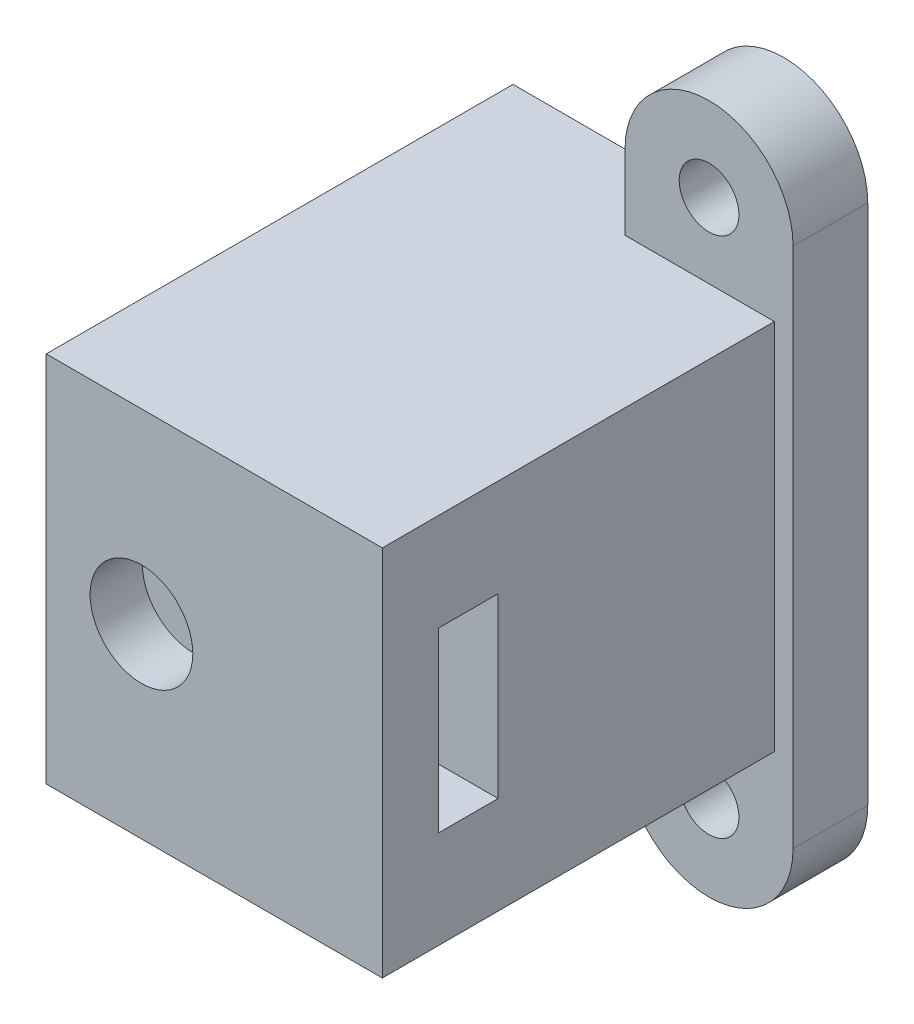
SolidWorks part; units mm, degrees
material "ABS"
ref_plane "Front Plane" through (0, 0, 0) normal (0, 0, 1) x (1, 0, 0)
ref_plane "Top Plane" through (0, 0, 0) normal (0, 1, 0) x (1, 0, 0)
ref_plane "Right Plane" through (0, 0, 0) normal (1, 0, 0) x (0, 0, -1)
sketch "Sketch1" plane through (0, 0, 0) normal (0, 0, 1) x (1, 0, 0)
  line L0 (0, 2.3958) -> (-1.763, 2.3958)
  line L1 (0, 9.975) -> (18, 9.975)
  line L2 (0, 9.975) -> (0, 2.3958)
  line L3 (0, -9.975) -> (18, -9.975)
  line L4 (18, 9.975) -> (18, -9.975)
  line L5 (-2.2551, 2.9838) -> (-1.9368, 4.7637)
  line L6 (-3.3312, 5.2591) -> (-5, 2.2458)
  line L7 (-5, 2.2458) -> (-5, 0.8958)
  line L8 (0, 0) -> (18, 0) construction
  line L9 (0, 0.8958) -> (-5, 0.8958)
  line L10 (0, -0.8958) -> (-5, -0.8958)
  line L11 (-5, -2.2458) -> (-5, -0.8958)
  line L12 (-3.3312, -5.2591) -> (-5, -2.2458)
  line L13 (-2.2551, -2.9838) -> (-1.9368, -4.7637)
  line L14 (0, -2.3958) -> (-1.763, -2.3958)
  line L15 (0, 0.8958) -> (0, -0.8958)
  line L16 (0, -2.3958) -> (0, -9.975)
  arc A0 (-1.9368, 4.7637) -> (-3.3312, 5.2591) centre (-2.6751, 4.8958) ccw
  arc A1 (-1.763, 2.3958) -> (-2.2551, 2.9838) centre (-1.763, 2.8958) cw
  arc A2 (-1.763, -2.3958) -> (-2.2551, -2.9838) centre (-1.763, -2.8958) ccw
  arc A3 (-1.9368, -4.7637) -> (-3.3312, -5.2591) centre (-2.6751, -4.8958) cw
  point P11 (0, 0)
  dimension "D1" = 0.5
  dimension "D2" = 0.75
  dimension "D3" = 19.95
  dimension "D4" = 2.6751
  dimension "D5" = 1.763
  dimension "D6" = 2
  dimension "D7" = 1.5
  dimension "D8" = 7.5792
  dimension "D9" = 5
  dimension "D10" = 1.35
  dimension "D11" = 18
extrude "Boss-Extrude1" add sketch "Sketch1" along normal blind 25
sketch "Sketch2" plane through (0, 0, 0) normal (-1, 0, 0) x (0, 0, 1)
  line L0 (22, 0) -> (25, 0) construction
  line L1 (22, -4.75) -> (18.8, -4.75)
  line L2 (22, -4.75) -> (22, 4.75)
  line L3 (22, 4.75) -> (18.8, 4.75)
  line L4 (18.8, -4.75) -> (18.8, 4.75)
  line L5 (25, 0.8958) -> (25, -0.8958) construction
  dimension "D1" = 3.2
  dimension "D2" = 9.5
  dimension "D3" = 3
extrude "Cut-Extrude1" cut sketch "Sketch2" against normal mid plane 111
sketch "Sketch3" plane through (0, 0, 25) normal (0, 0, 1) x (1, 0, 0)
  line L0 (5.1, -0.01) -> (0, 0) construction
  line L1 (0, 0.8958) -> (0, -0.8958) construction
  circle A0 centre (5.1, -0.01) radius 2.75
  dimension "D2" = 5.5
  dimension "D1" = 5.1
extrude "Cut-Extrude2" cut sketch "Sketch3" against normal blind 37 contours A0
sketch "Sketch4" plane through (0, 0, 0) normal (0, 0, -1) x (-1, 0, 0)
  line L1 (-10.556, -0.01) -> (-7.828, -4.735)
  line L2 (-7.828, -4.735) -> (-2.372, -4.735)
  line L3 (-2.372, -4.735) -> (0.356, -0.01)
  line L4 (0.356, -0.01) -> (-2.372, 4.715)
  line L5 (-2.372, 4.715) -> (-7.828, 4.715)
  line L6 (-7.828, 4.715) -> (-10.556, -0.01)
  circle A0 centre (-5.1, -0.01) radius 4.725 construction
  circle A1 centre (-5.1, -0.01) radius 2.75 construction
  dimension "D1" = 9.45
extrude "Cut-Extrude3" cut sketch "Sketch4" against normal blind 17
sketch "Sketch5" plane through (0, 0, 0) normal (0, 0, -1) x (-1, 0, 0)
  line L0 (-14.5, 0) -> (0, 0) construction
  circle A0 centre (-14.5, 0) radius 2.2
  dimension "D2" = 4.4
  dimension "D1" = 14.5
extrude "Cut-Extrude4" [suppressed] cut sketch "Sketch5" against normal blind 6.7
sketch "Sketch6" [suppressed] plane through (0, 0, 6.7) normal (0, 0, -1) x (-1, 0, 0)
  circle A0 centre (-14.5, 0) radius 5.2
  circle A1 centre (-14.5, 0) radius 2.2 construction
  dimension "D1" = 10.4
extrude "Cut-Extrude5" [suppressed] cut sketch "Sketch6" against normal blind 1.6
sketch "Sketch7" [suppressed] plane through (0, 0, 0) normal (0, 0, -1) x (-1, 0, 0)
  line L0 (-18, -9.975) -> (-18, 9.975) construction
  line L1 (-14.5, -2.2) -> (-18, -2.2)
  line L2 (-14.5, -2.2) -> (-14.5, 2.2)
  line L3 (-14.5, 2.2) -> (-18, 2.2)
  line L4 (-18, -2.2) -> (-18, 2.2)
  circle A0 centre (-14.5, 0) radius 2.2 construction
  point P8 (-14.5, 0)
extrude "Cut-Extrude6" [suppressed] cut sketch "Sketch7" against normal up to vertex
sketch "Sketch8" [suppressed] plane through (0, 0, 6.7) normal (0, 0, 1) x (1, 0, 0)
  line L0 (18, -9.975) -> (18, -2.2) construction
  line L1 (14.5, -5.2) -> (18, -5.2)
  line L2 (14.5, -5.2) -> (14.5, 5.2)
  line L3 (14.5, 5.2) -> (18, 5.2)
  line L4 (18, -5.2) -> (18, 5.2)
  arc A0 (9.5837, -1.694) -> (18, -3.8458) centre (14.5, 0) ccw construction
  arc A1 (18, 3.8458) -> (9.5794, 1.6815) centre (14.5, 0) ccw construction
  point P12 (14.5, 0)
extrude "Cut-Extrude7" [suppressed] cut sketch "Sketch8" along normal up to vertex
sketch "Sketch9" plane through (0, 0, 0) normal (-1, 0, 0) x (0, 0, 1)
  line L0 (25, -9.975) -> (0, -9.975) construction
  line L1 (25, 9.975) -> (18.8, 9.975)
  line L2 (25, 9.975) -> (25, -9.975)
  line L3 (25, -9.975) -> (18.8, -9.975)
  line L4 (18.8, 9.975) -> (18.8, -9.975)
  line L5 (18.8, -4.75) -> (18.8, -2.3958) construction
extrude "Cut-Extrude8" cut sketch "Sketch9" along normal blind 18
sketch "Sketch10" plane through (0, 0, 17) normal (0, 0, -1) x (-1, 0, 0)
  circle A0 centre (-5.1, -0.01) radius 2.75
extrude "Boss-Extrude2" add sketch "Sketch10" against normal blind 0.2
sketch "Sketch11" plane through (0, 0, 22) normal (0, 0, -1) x (-1, 0, 0)
  circle A0 centre (-5.1, -0.01) radius 2.75
extrude "Boss-Extrude3" add sketch "Sketch11" against normal blind 0.2
sketch "Sketch12" plane through (0, 0, 0) normal (0, 0, -1) x (-1, 0, 0)
  line L0 (-14.5, 0) -> (-18, 0) construction
  line L1 (-10, 4.4837) -> (-12, 0)
  line L2 (-10, -13.975) -> (-10, -4.4837)
  line L3 (-12, 0) -> (-10, -4.4837)
  line L4 (-19, -13.975) -> (-19, 13.975)
  line L5 (-10, -13.975) -> (-19, 13.975) construction
  line L6 (-10, 13.975) -> (-19, -13.975) construction
  line L7 (-18, -9.975) -> (-18, 9.975) construction
  line L8 (-10, 4.4837) -> (-10, 13.975)
  line L9 (-14.5, -13.975) -> (-14.5, 0) construction
  line L10 (-14.5, 0) -> (-14.5, 13.975) construction
  line L11 (0, -2.3958) -> (0, -9.975) construction
  line L12 (-18, 9.975) -> (0, 9.975) construction
  arc A0 (-19, -13.975) -> (-10, -13.975) centre (-14.5, -13.975) ccw
  arc A1 (-10, 13.975) -> (-19, 13.975) centre (-14.5, 13.975) ccw
  circle A2 centre (-14.5, -13.975) radius 1.6
  circle A3 centre (-14.5, 13.975) radius 1.6
  point P0 (-14.5, 0)
  dimension "D2" = 3.2
  dimension "D1" = 14.5
  dimension "D3" = 4
  dimension "D4" = 9
  dimension "D5" = 2
extrude "Boss-Extrude4" add sketch "Sketch12" against normal blind 4
